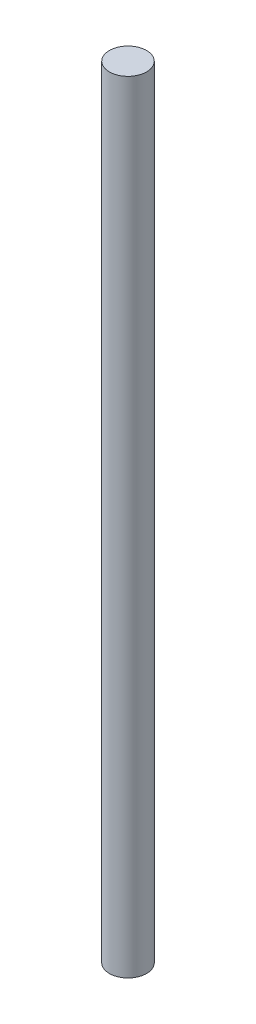
SolidWorks part; units mm, degrees
ref_plane "Alzado" through (0, 0, 0) normal (0, 0, 1) x (1, 0, 0)
ref_plane "Planta" through (0, 0, 0) normal (0, 1, 0) x (1, 0, 0)
ref_plane "Vista lateral" through (0, 0, 0) normal (1, 0, 0) x (0, 0, -1)
sketch "Croquis1" plane through (0, 0, 0) normal (0, 1, 0) x (1, 0, 0)
  circle A0 centre (0, 0) radius 4
  dimension "D1" = 8
extrude "Saliente-Extruir1" add sketch "Croquis1" along normal blind 168
